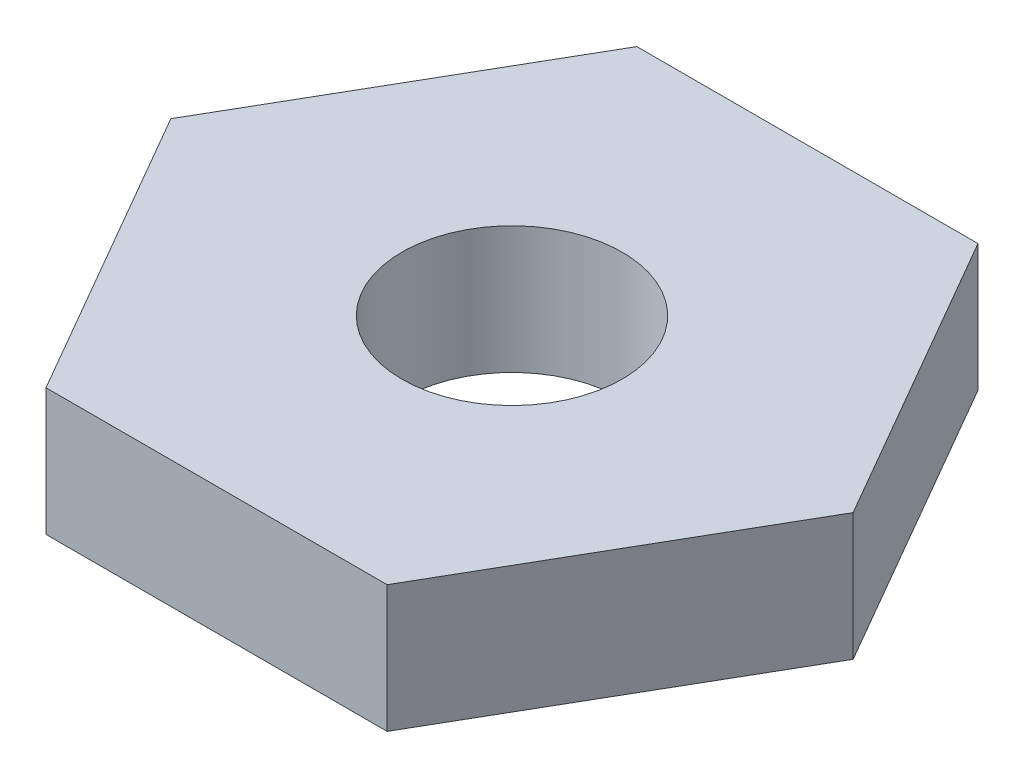
SolidWorks part; units mm, degrees
ref_plane "Front Plane" through (0, 0, 0) normal (0, 0, 1) x (1, 0, 0)
ref_plane "Top Plane" through (0, 0, 0) normal (0, 1, 0) x (1, 0, 0)
ref_plane "Right Plane" through (0, 0, 0) normal (1, 0, 0) x (0, 0, -1)
sketch "Sketch1" plane through (0, 0, 0) normal (0, 1, 0) x (1, 0, 0)
  line L7 (10.2295, 0) -> (5.1148, 8.859)
  line L8 (5.1148, 8.859) -> (-5.1148, 8.859)
  line L9 (-5.1148, 8.859) -> (-10.2295, 0)
  line L10 (-10.2295, 0) -> (-5.1148, -8.859)
  line L11 (-5.1148, -8.859) -> (5.1148, -8.859)
  line L12 (5.1148, -8.859) -> (10.2295, 0)
  circle A1 centre (0, 0) radius 3.302
  circle A2 centre (0, 0) radius 8.859 construction
  dimension "D2" = 6.604
extrude "Boss-Extrude1" add sketch "Sketch1" along normal blind 3.81
